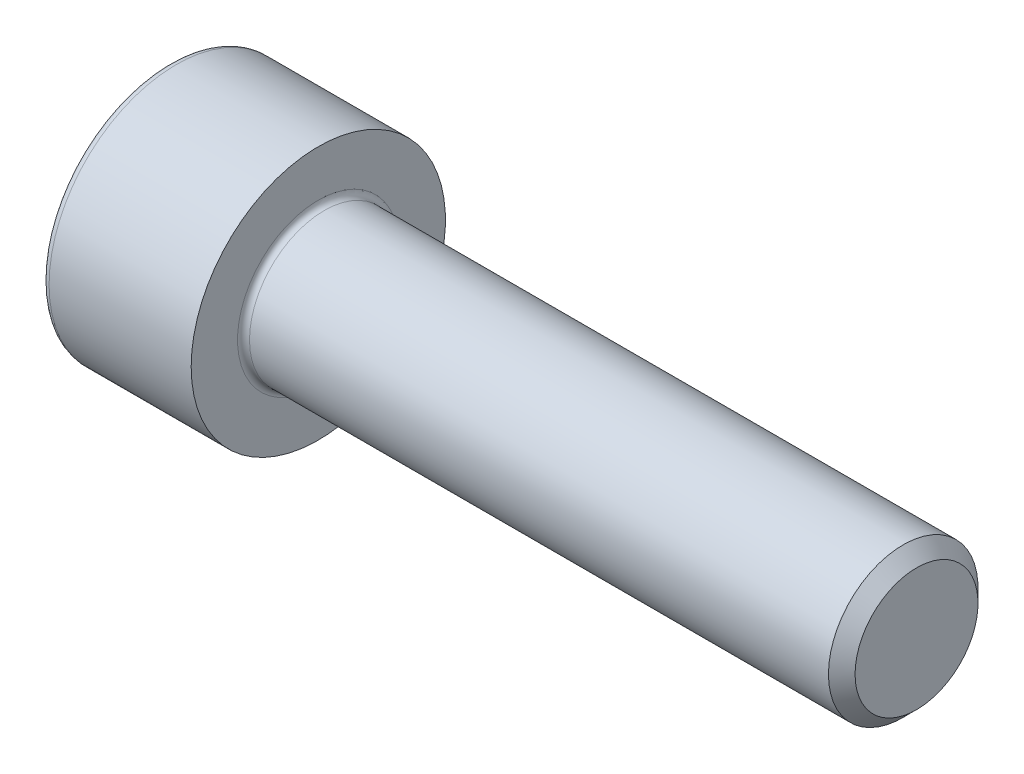
SolidWorks part; units mm, degrees
revolve "Base-Revolve" add sketch "BodySke"
sketch "BodySke" plane through (0, 0, 0) normal (0, 0, 1) x (1, 0, 0)
  line L0 (0, 0) -> (0, 4.25)
  line L1 (0, 4.25) -> (5, 4.25)
  line L2 (5, 4.25) -> (5, 2.5)
  line L3 (5, 2.5) -> (24.555, 2.5)
  line L4 (25, 2.055) -> (25, 0)
  line L5 (25, 0) -> (0, 0)
  line L6 (-31.75, 0) -> (127, 0) construction
  line L8 (25, 2.055) -> (24.555, 2.5)
  line L10 (25, -2.055) -> (24.555, -2.5) construction
  line L11 (5.8, 9.525) -> (5.8, 3.175) construction
  line L12 (5, 9.525) -> (5, 3.175) construction
  line L13 (-35, 9.525) -> (-35, 3.175) construction
  dimension "Head_ht" = 5
  dimension "Length" = 20
  dimension "Body_ch_ang" = 45
  dimension "Diameter" = 5
  dimension "Minor_dia" = 4.11
  dimension "Advance" = 0.8
  dimension "Thread_nom" = 20
  dimension "Thread_length" = 60
  dimension "Head_dia" = 8.5
cosmetic thread "ThreadCosmetic" [suppressed]
fillet "Fillet1" radius 0.2 1 edges at (5, 0, 2.5)
fillet "Fillet2" radius 0.25 1 edges at (0, 0, 4.25)
material "AISI 304"
ref_plane "Plane1" through (0, 0, 0) normal (0, 0, 1) x (1, 0, 0)
ref_plane "Plane2" through (0, 0, 0) normal (0, 1, 0) x (1, 0, 0)
ref_plane "Plane3" through (0, 0, 0) normal (1, 0, 0) x (0, 0, -1)
other "Configuration Table"
sketch "Sketch2" plane through (0, 0, 0) normal (0, 0, 1) x (1, 0, 0)
  line L0 (0, 2.042) -> (2.5, 2.042)
  line L1 (2.5, 2.042) -> (3.6789, 0)
  line L2 (-31.75, 0) -> (127, 0) construction
  line L3 (3.6789, 0) -> (0, 0)
  line L4 (0, 0) -> (0, 2.042)
  line L6 (0, 0) -> (47.625, 0) construction
  dimension "D1" = 2.042
  dimension "D2" = 60
  dimension "Depth" = 2.5
revolve "Hex-PreBroach" cut sketch "Sketch2" angle 360 about L6
sketch "Sketch3" plane through (0, 0, 0) normal (-1, 0, 0) x (0, 0.5, 0.866)
  line L0 (1.1789, 2.042) -> (-1.1789, 2.042)
  line L1 (-1.1789, 2.042) -> (-2.3579, 0)
  line L2 (1.1789, 2.042) -> (2.3579, 0)
  line L3 (1.1789, -2.042) -> (2.3579, 0)
  line L4 (1.1789, -2.042) -> (-1.1789, -2.042)
  line L5 (-1.1789, -2.042) -> (-2.3579, 0)
  dimension "D1" = 2.042
  dimension "D2" = 2.042
  dimension "Hex_size" = 4.084
extrude "Hex" cut sketch "Sketch3" against normal blind 2.5
sketch "ThdSchSke" plane through (0, 0, 0) normal (0, 0, 1) x (1, 0, 0)
  line L0 (7.4, -2.055) -> (7.0884, -2.5)
  line L1 (7.4, -2.055) -> (7.7116, -2.5)
  line L2 (7.7116, -2.5) -> (7.7116, -3.125)
  line L3 (-3.175, 0) -> (5.1513, 0) construction
  line L4 (0, 4) -> (0, -4) construction
  line L5 (7.7116, -3.125) -> (7.0884, -3.125)
  line L6 (7.0884, -3.125) -> (7.0884, -2.5)
  dimension "Thread_minor" = 4.11
  dimension "Diameter" = 5
  dimension "Start" = 7.4
revolve "ThreadSchematic" [suppressed] cut sketch "ThdSchSke" angle 360 about L3
pattern_linear "ThdSchPat" [suppressed]
equation "\"D2@Sketch3\" = \"Hex_size@Sketch3\" / 2"
equation "\"D1@Sketch3\" = \"Hex_size@Sketch3\" / 2"
equation "\"D1@Sketch2\" = \"Hex_size@Sketch3\" / 2"
equation "\"Thread_minor@ThreadCosmetic\"  =  \"Minor_dia@BodySke\""
equation "\"Depth@Sketch2\" =  \"Key_eng@Hex\""
equation "\"Thread_length@ThreadCosmetic\" = ((sgn( (\"Length@BodySke\" - \"Advance@BodySke\" * 3.0) - \"Thread_nom@BodySke\" )-1)*( (\"Length@BodySke\" - \"Advance@BodySke\" * 3.0) - \"Thread_nom@BodySke\" ))/-2+ \"Thread_nom@BodySke\""
equation "\"Thread_minor@ThdSchSke\" = \"Minor_dia@BodySke\""
equation "\"Diameter@ThdSchSke\" = \"Diameter@BodySke\""
equation "\"Overcut@ThdSchSke\" = \"Diameter@BodySke\" * 1.25"
equation "\"Start@ThdSchSke\" = \"Head_ht@BodySke\" + \"Length@BodySke\" - \"Thread_length@ThreadCosmetic\"  '---Non-countersunk---"
equation "\"Num_threads@ThdSchPat\" = int( \"Thread_length@ThreadCosmetic\" / \"Advance@BodySke\" + 0.999 )  + 1"
equation "\"Advance@ThdSchPat\" = \"Thread_length@ThreadCosmetic\" /  (\"Num_threads@ThdSchPat\" - 1) 'relax it"
equation "\"Num_threads@ThdSchPat\" = \"Num_threads@ThdSchPat\" - sgn( \"Num_threads@ThdSchPat\" - 1) '---chamfered tips only---"
